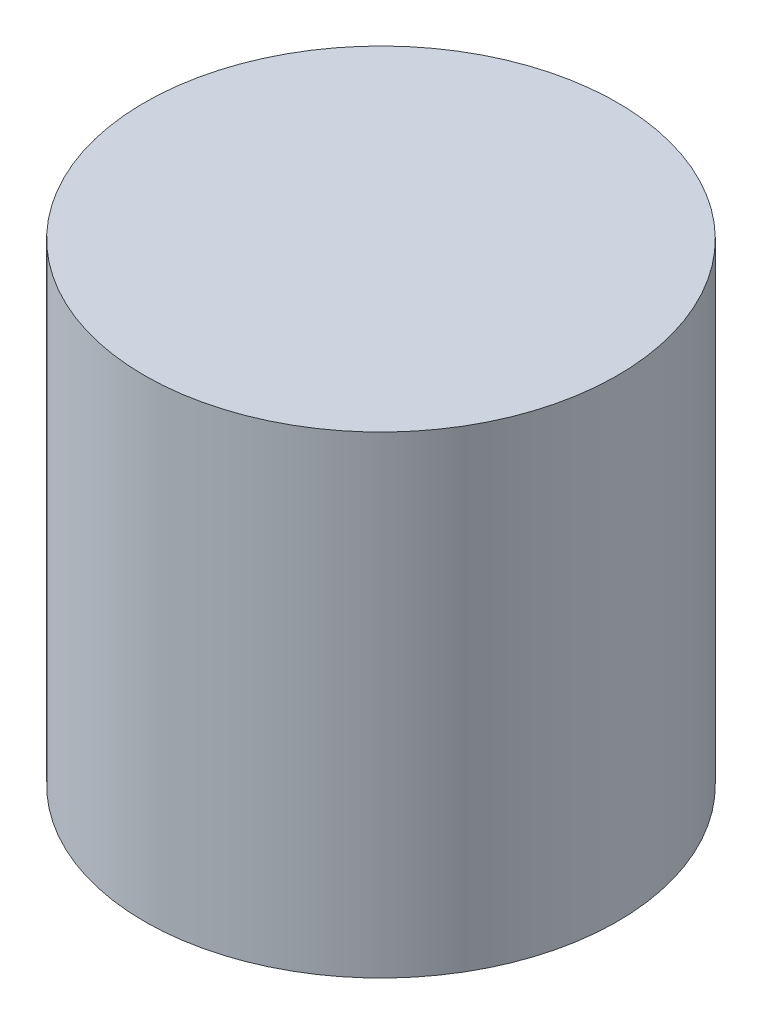
SolidWorks part; units mm, degrees
material "Stainless Steel (ferritic)"
ref_plane "Front Plane" through (0, 0, 0) normal (0, 0, 1) x (1, 0, 0)
ref_plane "Top Plane" through (0, 0, 0) normal (0, 1, 0) x (1, 0, 0)
ref_plane "Right Plane" through (0, 0, 0) normal (1, 0, 0) x (0, 0, -1)
sketch "Sketch2" plane through (0, 0, 0) normal (1, 0, 0) x (0, 0, -1)
  line L0 (-5, -12) -> (-6, -12)
  line L1 (-6, -12) -> (-6, 0)
  line L6 (-5.055, -9.0005) -> (-5, -12)
  line L7 (0, 88.1325) -> (0, -71.5922) construction
  line L8 (-6, 0) -> (0, 0)
  line L10 (0, 0) -> (0, -8.3737)
  line L11 (0, -8.3737) -> (-1.5, -8.3737)
  line L12 (-5.055, -9.0005) -> (-1.5, -8.3737)
  point P5 (-5.5, -12)
  dimension "D1" = 1.5
  dimension "D2" = 12
  dimension "D3" = 3
  dimension "D4" = 6
  dimension "D5" = 1
  dimension "D6" = 2.9995
  dimension "D7" = 170
  dimension "D8" = 8.3737
  dimension "D9" = 3.6263
revolve "Revolve1" add sketch "Sketch2" angle 360 about L7
sketch "Sketch5" plane through (0, -8.3737, 0) normal (0, -1, 0) x (-1, 0, 0)
  point P0 (0, 0)
hole_wizard "M3x0.5 Tapped Hole2" positions "Sketch5" profile "Sketch6" tap size "M3x0.5" standard "ANSI Metric"
sketch "Sketch6" plane through (0, -8.3737, 0) normal (1, 0, 0) x (0, 0, -1)
  line L0 (0, 0) -> (0, 5.6211)
  line L1 (0, 5.6211) -> (1.25, 4.87)
  line L2 (1.25, 4.87) -> (1.25, 0)
  line L5 (1.25, 0) -> (0, 0)
  line L10 (0, 5.6211) -> (-1.25, 4.87) construction
  line L11 (0, -6.35) -> (0, 107.95) construction
  dimension "Tap Drill Dia." = 2.5
  dimension "Tap Drill Depth" = 4.87
  dimension "Drill Angle" = 118
cosmetic thread "Hole Thread5" parameters "D1"=4.87, "D2"=3
